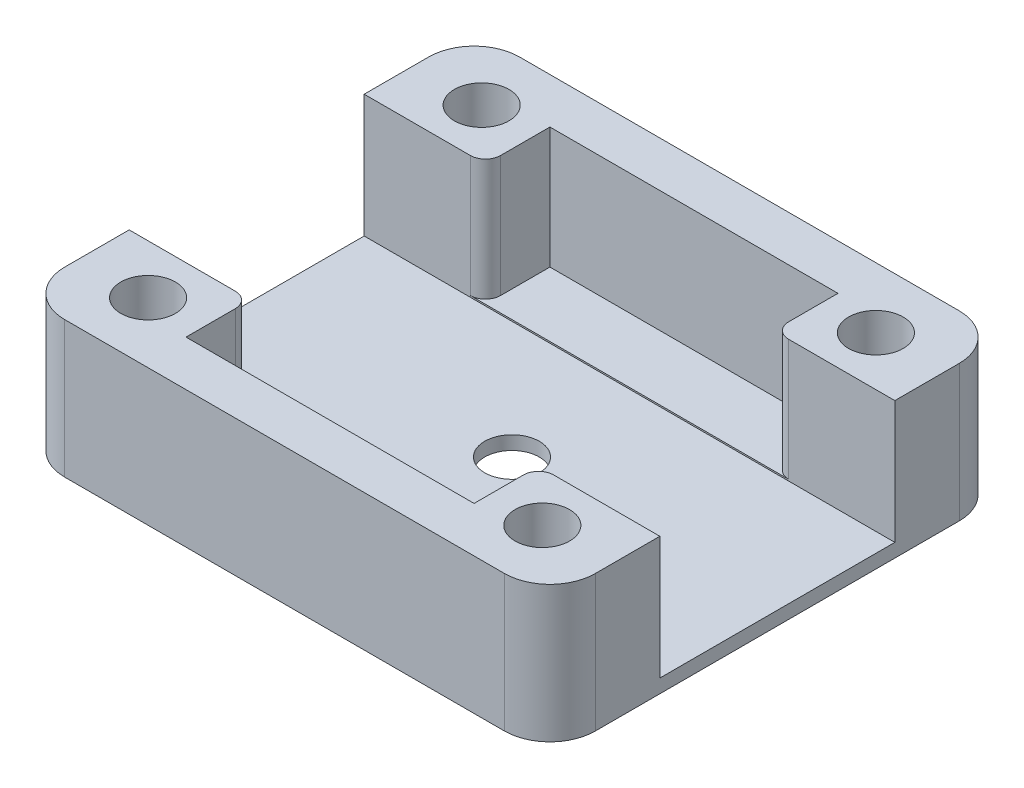
SolidWorks part; units mm, degrees
ref_plane "Front Plane" through (0, 0, 0) normal (0, 0, 1) x (1, 0, 0)
ref_plane "Top Plane" through (0, 0, 0) normal (0, 1, 0) x (1, 0, 0)
ref_plane "Right Plane" through (0, 0, 0) normal (1, 0, 0) x (0, 0, -1)
sketch "Sketch1" plane through (0, 0, 0) normal (0, 1, 0) x (1, 0, 0)
  line L1 (-17.5, -15) -> (17.5, -15)
  line L2 (-17.5, -15) -> (-17.5, 15)
  line L3 (-17.5, 15) -> (17.5, 15)
  line L4 (17.5, -15) -> (17.5, 15)
  line L5 (-17.5, -15) -> (17.5, 15) construction
  line L6 (-17.5, 15) -> (17.5, -15) construction
  point P0 (0, 0)
  dimension "D1" = 35
  dimension "D2" = 30
extrude "Boss-Extrude1" add sketch "Sketch1" along normal blind 9
sketch "Sketch3" plane through (0, 9, 0) normal (0, 1, 0) x (1, 0, 0)
  line L8 (14.5, -12) -> (14.5, 12)
  line L9 (14.5, 12) -> (-14.5, 12)
  line L10 (-14.5, 12) -> (-14.5, -12)
  line L11 (-14.5, -12) -> (14.5, -12)
  line L12 (14.5, -12) -> (14.5, 12)
  line L13 (14.5, 12) -> (-14.5, 12)
  line L14 (-14.5, 12) -> (-14.5, -12)
  line L15 (-14.5, -12) -> (14.5, -12)
  dimension "D1" = 3
extrude "Cut-Extrude1" cut sketch "Sketch3" against normal blind 8
sketch "Sketch4" plane through (-17.5, 0, 0) normal (-1, 0, 0) x (0, 0, 1)
  line L0 (-15, 0) -> (15, 0) construction
  line L1 (-7.75, 0.9) -> (7.75, 0.9)
  line L2 (-7.75, 0.9) -> (-7.75, 9)
  line L3 (-7.75, 9) -> (7.75, 9)
  line L4 (7.75, 0.9) -> (7.75, 9)
  line L5 (-7.75, 0.9) -> (7.75, 9) construction
  line L6 (-7.75, 9) -> (7.75, 0.9) construction
  line L7 (-15, 9) -> (15, 9) construction
  point P0 (0, 4.95)
  point P8 (0, 0)
  dimension "D1" = 8.1
  dimension "D2" = 15.5
extrude "Cut-Extrude2" cut sketch "Sketch4" against normal through all
sketch "Sketch5" plane through (0, 1, 0) normal (0, 1, 0) x (1, 0, 0)
  line L0 (14.5, 7.75) -> (-14.5, 7.75) construction
  line L1 (-14.5, 12) -> (-9.5, 12)
  line L2 (-14.5, 12) -> (-14.5, 7.75)
  line L3 (-14.5, 7.75) -> (-9.5, 7.75)
  line L4 (-9.5, 12) -> (-9.5, 7.75)
  line L5 (-14.5, -7.75) -> (14.5, -7.75) construction
  line L6 (14.5, 12) -> (9.5, 12)
  line L7 (14.5, 12) -> (14.5, 7.75)
  line L8 (14.5, 7.75) -> (9.5, 7.75)
  line L9 (9.5, 12) -> (9.5, 7.75)
  line L10 (14.5, -12) -> (9.5, -12)
  line L11 (14.5, -12) -> (14.5, -7.75)
  line L12 (14.5, -7.75) -> (9.5, -7.75)
  line L13 (9.5, -12) -> (9.5, -7.75)
  line L15 (-14.5, -12) -> (-9.5, -12)
  line L16 (-14.5, -12) -> (-14.5, -7.75)
  line L17 (-14.5, -7.75) -> (-9.5, -7.75)
  line L18 (-9.5, -12) -> (-9.5, -7.75)
  dimension "D1" = 5
extrude "Boss-Extrude2" add sketch "Sketch5" along normal up to surface (8 mm away) up to face at (0, 9, -10.625)
hole_wizard "M3 Clearance Hole1" positions "Sketch6" profile "Sketch7" hole size "M3" standard "ANSI Metric" end condition through all
sketch "Sketch6" plane through (0, 9, 0) normal (0, 1, 0) x (1, 0, 0)
  line L1 (-13, -11) -> (13, -11)
  line L2 (-13, -11) -> (-13, 11)
  line L3 (-13, 11) -> (13, 11)
  line L4 (13, -11) -> (13, 11)
  line L5 (-13, -11) -> (13, 11) construction
  line L6 (-13, 11) -> (13, -11) construction
  point P1 (0, 0)
  point P2 (13, 11)
  point P73 (-13, -11)
  point P74 (-13, 11)
  point P75 (13, -11)
  dimension "D1" = 26
  dimension "D2" = 22
sketch "Sketch7" plane through (0, 9, 0) normal (1, 0, 0) x (0, 0, 1)
  line L0 (0, 0) -> (0, 9)
  line L1 (0, 9) -> (1.8, 9)
  line L2 (1.8, 9) -> (1.8, 0)
  line L5 (1.8, 0) -> (0, 0)
  line L11 (0, -6.35) -> (0, 107.95) construction
  dimension "Thru Hole Dia." = 3.6
  dimension "Thru Hole Depth" = 9
fillet "Fillet1" radius 3 4 edges at (-17.5, 4.5, 15) (17.5, 4.5, 15) (17.5, 4.5, -15) (-17.5, 4.5, -15)
fillet "Fillet2" radius 1 4 edges at (9.5, 5, 7.75) (-9.5, 5, 7.75) (-9.5, 5, -7.75) (9.5, 5, -7.75)
